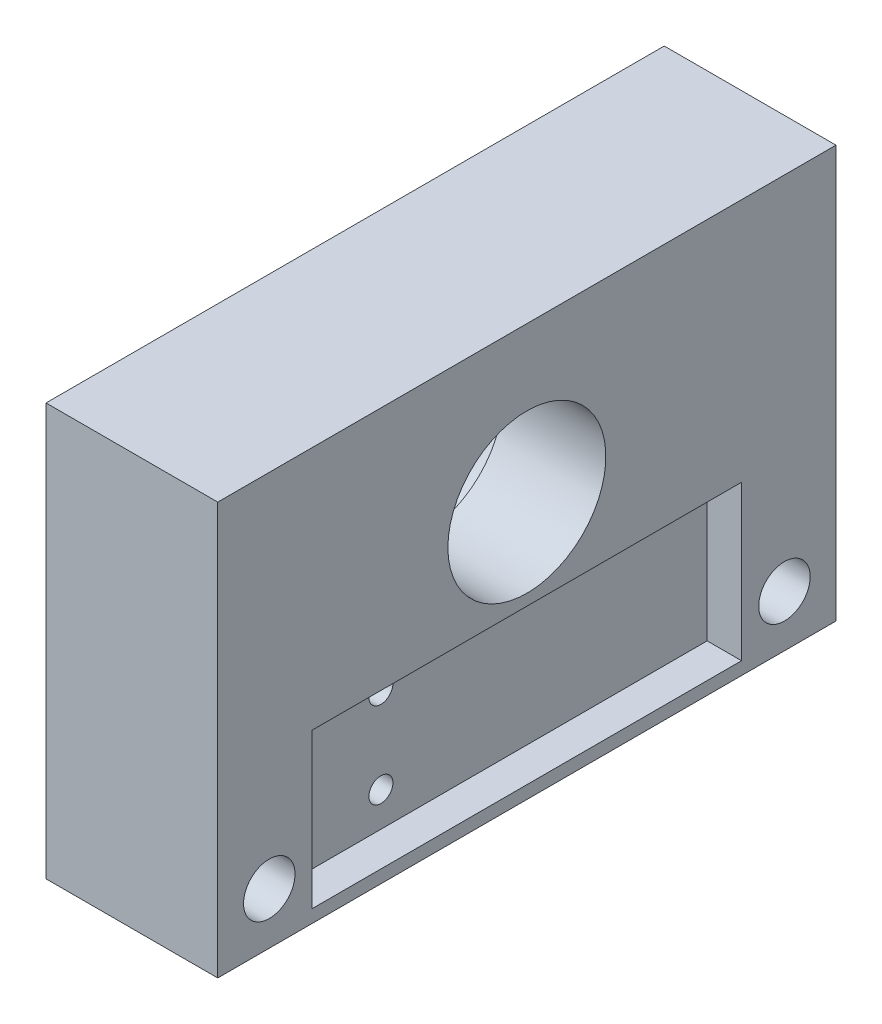
SolidWorks part; units mm, degrees
other "标注1"
sketch "草图18" plane through (10, -24, -36) normal (0.9451, -0.0152, -0.3265) x (-0.3269, -0.0361, -0.9444)
ref_plane "前视基准面" through (0, 0, 0) normal (0, 0, 1) x (1, 0, 0)
ref_plane "上视基准面" through (0, 0, 0) normal (0, 1, 0) x (1, 0, 0)
ref_plane "右视基准面" through (0, 0, 0) normal (1, 0, 0) x (0, 0, -1)
sketch "草图1" plane through (0, 0, 0) normal (1, 0, 0) x (0, 0, -1)
  line L1 (0, 0) -> (36, 0)
  line L2 (0, 0) -> (0, -24)
  line L3 (0, -24) -> (36, -24)
  line L4 (36, 0) -> (36, -24)
  dimension "D1" = 36
  dimension "D2" = 24
extrude "凸台-拉伸1" add sketch "草图1" along normal blind 10
sketch "草图2" plane through (0, 0, 0) normal (-1, 0, 0) x (0, 0, 1)
  line L0 (-18, -9) -> (-18, 0) construction
  line L1 (-36, 0) -> (0, 0) construction
  line L2 (0, -24) -> (-36, -24) construction
  circle A0 centre (-18, -9) radius 6.05
  dimension "D1" = 12.1
  dimension "D2" = 15
extrude "切除-拉伸1" cut sketch "草图2" against normal blind 4
sketch "草图3" plane through (4, 0, 0) normal (-1, 0, 0) x (0, 0, 1)
  circle A0 centre (-18, -9) radius 4.6
  dimension "D1" = 9.2
extrude "切除-拉伸2" cut sketch "草图3" against normal through all
sketch "草图5" plane through (0, -24, 0) normal (0, -1, 0) x (-1, 0, 0)
  line L0 (-5, 36) -> (-5, 28) construction
  line L1 (-10, 36) -> (0, 36) construction
  line L3 (-5, 8) -> (-5, 0) construction
  line L4 (-10, 0) -> (0, 0) construction
  circle A0 centre (-5, 28) radius 2.5
  circle A1 centre (-5, 8) radius 2.5
  dimension "D2" = 5
  dimension "D1" = 20
extrude "切除-拉伸4" cut sketch "草图5" against normal blind 8
sketch "草图7" plane through (10, 0, 0) normal (1, 0, 0) x (0, 0, -1)
  line L0 (18, -13.5) -> (18, -14.25) construction
  line L1 (5.5, -14.25) -> (30.5, -14.25)
  line L2 (5.5, -14.25) -> (5.5, -23.25)
  line L3 (5.5, -23.25) -> (30.5, -23.25)
  line L4 (30.5, -14.25) -> (30.5, -23.25)
  line L5 (18, -23.25) -> (18, -24) construction
  line L6 (0, -24) -> (36, -24) construction
  dimension "D1" = 25
  dimension "D2" = 9
extrude "切除-拉伸5" cut sketch "草图7" against normal blind 2
sketch "草图8" plane through (0, 0, 0) normal (-1, 0, 0) x (0, 0, 1)
  line L0 (-26, -9) -> (-18, -9) construction
  line L1 (-18, -9) -> (-10, -9) construction
  circle A0 centre (-10, -9) radius 1.5
  circle A1 centre (-26, -9) radius 1.5
  dimension "D1" = 3
  dimension "D2" = 16
extrude "切除-拉伸6" cut sketch "草图8" against normal blind 5
sketch "草图9" plane through (10, 0, 0) normal (1, 0, 0) x (0, 0, -1)
  line L0 (0, -24) -> (36, -24) construction
  circle A0 centre (3, -21) radius 1.5
  circle A1 centre (33, -21) radius 1.5
  dimension "D2" = 3
  dimension "D1" = 30
  dimension "D3" = 3
extrude "切除-拉伸7" cut sketch "草图9" against normal blind 5
sketch "草图11" plane through (0, 0, 0) normal (-1, 0, 0) x (0, 0, 1)
  line L0 (0, -24) -> (-36, -24) construction
  line L1 (-36, 0) -> (-29, 0) construction
  line L2 (-36, 0) -> (-36, -24) construction
  line L3 (-36, -24) -> (-29, -24) construction
  line L4 (-29, 0) -> (-29, -24) construction
  line L5 (-32.5, -3) -> (-3.5, -3) construction
  line L6 (0, 0) -> (-7, 0) construction
  line L7 (0, 0) -> (0, -24) construction
  line L8 (0, -24) -> (-7, -24) construction
  line L9 (-7, 0) -> (-7, -24) construction
  line L10 (-3.5, -3) -> (-3.5, -21) construction
  line L11 (-3.5, -21) -> (-32.5, -21) construction
  line L12 (-32.5, -21) -> (-32.5, -3) construction
  line L13 (-32.5, 0) -> (-32.5, -3) construction
  line L14 (-3.5, 0) -> (-3.5, -3) construction
  line L15 (-36, 0) -> (0, 0) construction
  circle A0 centre (-32.5, -3) radius 1
  circle A1 centre (-32.5, -21) radius 1
  circle A2 centre (-3.5, -21) radius 1
  circle A3 centre (-3.5, -3) radius 1
  dimension "D3" = 2
  dimension "D1" = 7
  dimension "D2" = 7
  dimension "D4" = 3
  dimension "D5" = 3
extrude "切除-拉伸9" cut sketch "草图11" against normal blind 3
sketch "草图13" plane through (8, 0, 0) normal (1, 0, 0) x (0, 0, -1)
  line L0 (18, -14.25) -> (18, -16.25) construction
  line L1 (11.5, -16.25) -> (24.5, -16.25) construction
  line L2 (11.5, -16.25) -> (11.5, -21.25) construction
  line L3 (11.5, -21.25) -> (24.5, -21.25) construction
  line L4 (24.5, -16.25) -> (24.5, -21.25) construction
  line L5 (30.5, -14.25) -> (5.5, -14.25) construction
  line L6 (24.5, -18.75) -> (30.5, -18.75) construction
  line L7 (30.5, -23.25) -> (30.5, -14.25) construction
  circle A0 centre (11.5, -16.25) radius 0.7
  circle A1 centre (11.5, -21.25) radius 0.7
  dimension "D3" = 1.4
  dimension "D1" = 13
  dimension "D2" = 5
extrude "切除-拉伸10" cut sketch "草图13" against normal blind 5
